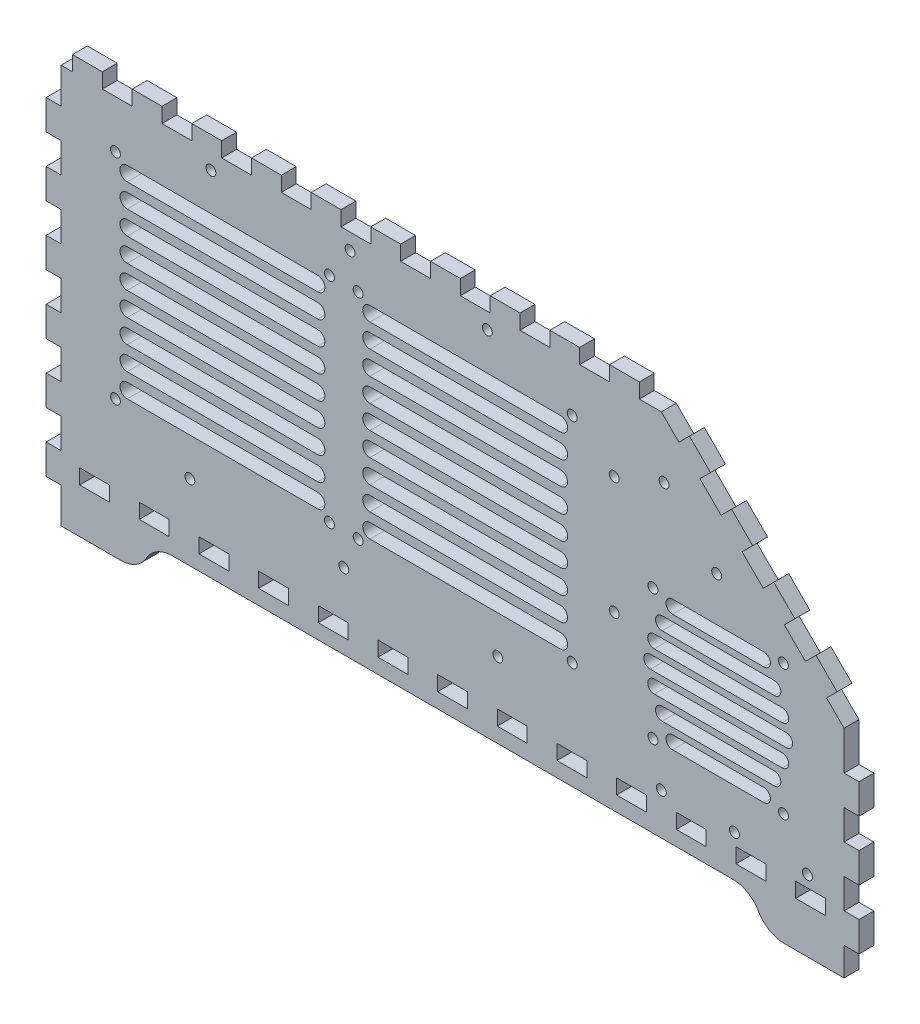
SolidWorks part; units mm, degrees
ref_plane "Front Plane" through (0, 0, 0) normal (0, 0, 1) x (1, 0, 0)
ref_plane "Top Plane" through (0, 0, 0) normal (0, 1, 0) x (1, 0, 0)
ref_plane "Right Plane" through (0, 0, 0) normal (1, 0, 0) x (0, 0, -1)
sketch "Model" plane through (0, 0, 0) normal (0, 0, 1) x (1, 0, 0)
  line L4 (28.9553, 40.0032) -> (23.2406, 40.0032)
  line L5 (23.2406, 40.0032) -> (23.2406, 45.7179)
  line L6 (23.2406, 45.7179) -> (34.67, 45.7179)
  line L7 (34.67, 45.7179) -> (34.67, 40.0032)
  line L8 (34.67, 40.0032) -> (28.9553, 40.0032)
  line L9 (51.8156, 40.0032) -> (46.0996, 40.0032)
  line L10 (46.0996, 40.0032) -> (46.0996, 45.7179)
  line L11 (46.0996, 45.7179) -> (57.5303, 45.7179)
  line L12 (57.5303, 45.7179) -> (57.5303, 40.0032)
  line L13 (57.5303, 40.0032) -> (51.8156, 40.0032)
  line L14 (74.6746, 40.0032) -> (68.9599, 40.0032)
  line L15 (68.9599, 40.0032) -> (68.9599, 45.7179)
  line L16 (68.9599, 45.7179) -> (80.3906, 45.7179)
  line L17 (80.3906, 45.7179) -> (80.3906, 40.0032)
  line L18 (80.3906, 40.0032) -> (74.6746, 40.0032)
  line L19 (97.5349, 40.0032) -> (91.8199, 40.0032)
  line L20 (91.8199, 40.0032) -> (91.8199, 45.7179)
  line L21 (91.8199, 45.7179) -> (103.25, 45.7179)
  line L22 (103.25, 45.7179) -> (103.25, 40.0032)
  line L23 (103.25, 40.0032) -> (97.5349, 40.0032)
  line L24 (120.395, 40.0032) -> (114.68, 40.0032)
  line L25 (114.68, 40.0032) -> (114.68, 45.7179)
  line L26 (114.68, 45.7179) -> (126.11, 45.7179)
  line L27 (126.11, 45.7179) -> (126.11, 40.0032)
  line L28 (126.11, 40.0032) -> (120.395, 40.0032)
  line L29 (143.255, 40.0032) -> (137.541, 40.0032)
  line L30 (137.541, 40.0032) -> (137.541, 45.7179)
  line L31 (137.541, 45.7179) -> (148.97, 45.7179)
  line L32 (148.97, 45.7179) -> (148.97, 40.0032)
  line L33 (148.97, 40.0032) -> (143.255, 40.0032)
  line L34 (166.116, 40.0032) -> (160.4, 40.0032)
  line L35 (160.4, 40.0032) -> (160.4, 45.7179)
  line L36 (160.4, 45.7179) -> (171.83, 45.7179)
  line L37 (171.83, 45.7179) -> (171.83, 40.0032)
  line L38 (171.83, 40.0032) -> (166.116, 40.0032)
  line L39 (188.975, 40.0032) -> (183.26, 40.0032)
  line L40 (183.26, 40.0032) -> (183.26, 45.7179)
  line L41 (183.26, 45.7179) -> (194.691, 45.7179)
  line L42 (194.691, 45.7179) -> (194.691, 40.0032)
  line L43 (194.691, 40.0032) -> (188.975, 40.0032)
  line L44 (211.835, 40.0032) -> (206.12, 40.0032)
  line L45 (206.12, 40.0032) -> (206.12, 45.7179)
  line L46 (206.12, 45.7179) -> (217.55, 45.7179)
  line L47 (217.55, 45.7179) -> (217.55, 40.0032)
  line L48 (217.55, 40.0032) -> (211.835, 40.0032)
  line L49 (234.695, 40.0032) -> (228.98, 40.0032)
  line L50 (228.98, 40.0032) -> (228.98, 45.7179)
  line L51 (228.98, 45.7179) -> (240.41, 45.7179)
  line L52 (240.41, 45.7179) -> (240.41, 40.0032)
  line L53 (240.41, 40.0032) -> (234.695, 40.0032)
  line L54 (257.555, 40.0032) -> (251.841, 40.0032)
  line L55 (251.841, 40.0032) -> (251.841, 45.7179)
  line L56 (251.841, 45.7179) -> (263.27, 45.7179)
  line L57 (263.27, 45.7179) -> (263.27, 40.0032)
  line L58 (263.27, 40.0032) -> (257.555, 40.0032)
  line L59 (280.416, 40.0032) -> (274.7, 40.0032)
  line L60 (274.7, 40.0032) -> (274.7, 45.7179)
  line L61 (274.7, 45.7179) -> (286.13, 45.7179)
  line L62 (286.13, 45.7179) -> (286.13, 40.0032)
  line L63 (286.13, 40.0032) -> (280.416, 40.0032)
  line L64 (303.275, 40.0032) -> (297.56, 40.0032)
  line L65 (297.56, 40.0032) -> (297.56, 45.7179)
  line L66 (297.56, 45.7179) -> (308.991, 45.7179)
  line L67 (308.991, 45.7179) -> (308.991, 40.0032)
  line L68 (308.991, 40.0032) -> (303.275, 40.0032)
  line L69 (16.1148, 22.8575) -> (38.9749, 22.8575)
  line L70 (38.9749, 22.8575) -> (39.3485, 22.8575)
  line L71 (39.3485, 22.8575) -> (40.4689, 22.9567)
  line L72 (40.4689, 22.9567) -> (41.9322, 23.2475)
  line L73 (41.9322, 23.2475) -> (43.3447, 23.7271)
  line L74 (43.3447, 23.7271) -> (44.366, 24.2025)
  line L75 (44.366, 24.2025) -> (44.6899, 24.3885)
  line L76 (44.6899, 24.3885) -> (44.8511, 24.4822)
  line L77 (44.8511, 24.4822) -> (45.3263, 24.7854)
  line L78 (45.3263, 24.7854) -> (45.9341, 25.2222)
  line L79 (45.9341, 25.2222) -> (46.5116, 25.6963)
  line L80 (46.5116, 25.6963) -> (47.056, 26.2062)
  line L81 (47.056, 26.2062) -> (47.5657, 26.7505)
  line L82 (47.5657, 26.7505) -> (48.0399, 27.3279)
  line L83 (48.0399, 27.3279) -> (48.4766, 27.9356)
  line L84 (48.4766, 27.9356) -> (48.7796, 28.411)
  line L85 (48.7796, 28.411) -> (48.8735, 28.5722)
  line L86 (48.8735, 28.5722) -> (48.9673, 28.7348)
  line L87 (48.9673, 28.7348) -> (49.2689, 29.2103)
  line L88 (49.2689, 29.2103) -> (49.7057, 29.818)
  line L89 (49.7057, 29.818) -> (50.1798, 30.3954)
  line L90 (50.1798, 30.3954) -> (50.6899, 30.9397)
  line L91 (50.6899, 30.9397) -> (51.2339, 31.4496)
  line L92 (51.2339, 31.4496) -> (51.8114, 31.9236)
  line L93 (51.8114, 31.9236) -> (52.4192, 32.3605)
  line L94 (52.4192, 32.3605) -> (52.8948, 32.6622)
  line L95 (52.8948, 32.6622) -> (53.0571, 32.756)
  line L96 (53.0571, 32.756) -> (53.3799, 32.9434)
  line L97 (53.3799, 32.9434) -> (54.4008, 33.4188)
  line L98 (54.4008, 33.4188) -> (55.8133, 33.8983)
  line L99 (55.8133, 33.8983) -> (57.2766, 34.1891)
  line L100 (57.2766, 34.1891) -> (58.3971, 34.287)
  line L101 (58.3971, 34.287) -> (58.7721, 34.287)
  line L102 (58.7721, 34.287) -> (273.458, 34.287)
  line L103 (273.458, 34.287) -> (273.831, 34.287)
  line L104 (273.831, 34.287) -> (274.952, 34.1891)
  line L105 (274.952, 34.1891) -> (276.415, 33.8983)
  line L106 (276.415, 33.8983) -> (277.828, 33.4188)
  line L107 (277.828, 33.4188) -> (278.849, 32.9434)
  line L108 (278.849, 32.9434) -> (279.172, 32.756)
  line L109 (279.172, 32.756) -> (279.334, 32.6636)
  line L110 (279.334, 32.6636) -> (279.809, 32.3605)
  line L111 (279.809, 32.3605) -> (280.417, 31.9236)
  line L112 (280.417, 31.9236) -> (280.995, 31.4496)
  line L113 (280.995, 31.4496) -> (281.539, 30.9397)
  line L114 (281.539, 30.9397) -> (282.049, 30.3954)
  line L115 (282.049, 30.3954) -> (282.523, 29.818)
  line L116 (282.523, 29.818) -> (282.96, 29.2103)
  line L117 (282.96, 29.2103) -> (283.263, 28.7348)
  line L118 (283.263, 28.7348) -> (283.356, 28.5722)
  line L119 (283.356, 28.5722) -> (283.449, 28.411)
  line L120 (283.449, 28.411) -> (283.752, 27.9356)
  line L121 (283.752, 27.9356) -> (284.189, 27.3279)
  line L122 (284.189, 27.3279) -> (284.663, 26.7505)
  line L123 (284.663, 26.7505) -> (285.172, 26.2062)
  line L124 (285.172, 26.2062) -> (285.717, 25.6963)
  line L125 (285.717, 25.6963) -> (286.294, 25.2222)
  line L126 (286.294, 25.2222) -> (286.902, 24.7854)
  line L127 (286.902, 24.7854) -> (287.377, 24.4822)
  line L128 (287.377, 24.4822) -> (287.54, 24.3885)
  line L129 (287.54, 24.3885) -> (287.862, 24.2025)
  line L130 (287.862, 24.2025) -> (288.884, 23.7271)
  line L131 (288.884, 23.7271) -> (290.296, 23.2475)
  line L132 (290.296, 23.2475) -> (291.76, 22.9567)
  line L133 (291.76, 22.9567) -> (292.88, 22.8575)
  line L134 (292.88, 22.8575) -> (293.255, 22.8575)
  line L135 (293.255, 22.8575) -> (316.115, 22.8575)
  line L136 (316.115, 22.8575) -> (316.115, 33.6917)
  line L137 (316.115, 33.6917) -> (321.83, 33.6917)
  line L138 (321.83, 33.6917) -> (321.83, 45.1224)
  line L139 (321.83, 45.1224) -> (316.115, 45.1224)
  line L140 (316.115, 45.1224) -> (316.115, 56.552)
  line L141 (316.115, 56.552) -> (321.83, 56.552)
  line L142 (321.83, 56.552) -> (321.83, 67.9813)
  line L143 (321.83, 67.9813) -> (316.115, 67.9813)
  line L144 (316.115, 67.9813) -> (316.115, 79.412)
  line L145 (316.115, 79.412) -> (321.83, 79.412)
  line L146 (321.83, 79.412) -> (321.83, 90.8417)
  line L147 (321.83, 90.8417) -> (316.115, 90.8417)
  line L148 (316.115, 90.8417) -> (316.115, 101.677)
  line L149 (316.115, 101.677) -> (316.115, 105.718)
  line L150 (316.115, 105.718) -> (309.403, 112.43)
  line L151 (309.403, 112.43) -> (313.444, 116.47)
  line L152 (313.444, 116.47) -> (305.362, 124.553)
  line L153 (305.362, 124.553) -> (301.321, 120.512)
  line L154 (301.321, 120.512) -> (293.238, 128.595)
  line L155 (293.238, 128.595) -> (297.28, 132.635)
  line L156 (297.28, 132.635) -> (289.198, 140.717)
  line L157 (289.198, 140.717) -> (285.156, 136.677)
  line L158 (285.156, 136.677) -> (277.074, 144.759)
  line L159 (277.074, 144.759) -> (281.114, 148.801)
  line L160 (281.114, 148.801) -> (273.032, 156.881)
  line L161 (273.032, 156.881) -> (268.992, 152.841)
  line L162 (268.992, 152.841) -> (260.91, 160.923)
  line L163 (260.91, 160.923) -> (264.951, 164.963)
  line L164 (264.951, 164.963) -> (256.869, 173.046)
  line L165 (256.869, 173.046) -> (252.827, 169.005)
  line L166 (252.827, 169.005) -> (246.115, 175.718)
  line L167 (246.115, 175.718) -> (242.074, 175.718)
  line L168 (242.074, 175.718) -> (237.68, 175.718)
  line L169 (237.68, 175.718) -> (237.68, 181.433)
  line L170 (237.68, 181.433) -> (226.249, 181.433)
  line L171 (226.249, 181.433) -> (226.249, 175.718)
  line L172 (226.249, 175.718) -> (214.82, 175.718)
  line L173 (214.82, 175.718) -> (214.82, 181.433)
  line L174 (214.82, 181.433) -> (203.389, 181.433)
  line L175 (203.389, 181.433) -> (203.389, 175.718)
  line L176 (203.389, 175.718) -> (191.959, 175.718)
  line L177 (191.959, 175.718) -> (191.959, 181.433)
  line L178 (191.959, 181.433) -> (180.53, 181.433)
  line L179 (180.53, 181.433) -> (180.53, 175.718)
  line L180 (180.53, 175.718) -> (169.099, 175.718)
  line L181 (169.099, 175.718) -> (169.099, 181.433)
  line L182 (169.099, 181.433) -> (157.67, 181.433)
  line L183 (157.67, 181.433) -> (157.67, 175.718)
  line L184 (157.67, 175.718) -> (146.239, 175.718)
  line L185 (146.239, 175.718) -> (146.239, 181.433)
  line L186 (146.239, 181.433) -> (134.809, 181.433)
  line L187 (134.809, 181.433) -> (134.809, 175.718)
  line L188 (134.809, 175.718) -> (123.38, 175.718)
  line L189 (123.38, 175.718) -> (123.38, 181.433)
  line L190 (123.38, 181.433) -> (111.949, 181.433)
  line L191 (111.949, 181.433) -> (111.949, 175.718)
  line L192 (111.949, 175.718) -> (100.52, 175.718)
  line L193 (100.52, 175.718) -> (100.52, 181.433)
  line L194 (100.52, 181.433) -> (89.0887, 181.433)
  line L195 (89.0887, 181.433) -> (89.0887, 175.718)
  line L196 (89.0887, 175.718) -> (77.6594, 175.718)
  line L197 (77.6594, 175.718) -> (77.6594, 181.433)
  line L198 (77.6594, 181.433) -> (66.2298, 181.433)
  line L199 (66.2298, 181.433) -> (66.2298, 175.718)
  line L200 (66.2298, 175.718) -> (54.7991, 175.718)
  line L201 (54.7991, 175.718) -> (54.7991, 181.433)
  line L202 (54.7991, 181.433) -> (43.3698, 181.433)
  line L203 (43.3698, 181.433) -> (43.3698, 175.718)
  line L204 (43.3698, 175.718) -> (31.9388, 175.718)
  line L205 (31.9388, 175.718) -> (31.9388, 181.433)
  line L206 (31.9388, 181.433) -> (20.5093, 181.433)
  line L207 (20.5093, 181.433) -> (20.5093, 175.718)
  line L208 (20.5093, 175.718) -> (16.1148, 175.718)
  line L209 (16.1148, 175.718) -> (16.1148, 162.153)
  line L210 (16.1148, 162.153) -> (10.4001, 162.153)
  line L211 (10.4001, 162.153) -> (10.4001, 150.723)
  line L212 (10.4001, 150.723) -> (16.1148, 150.723)
  line L213 (16.1148, 150.723) -> (16.1148, 139.292)
  line L214 (16.1148, 139.292) -> (10.4001, 139.292)
  line L215 (10.4001, 139.292) -> (10.4001, 127.863)
  line L216 (10.4001, 127.863) -> (16.1148, 127.863)
  line L217 (16.1148, 127.863) -> (16.1148, 116.433)
  line L218 (16.1148, 116.433) -> (10.4001, 116.433)
  line L219 (10.4001, 116.433) -> (10.4001, 105.003)
  line L220 (10.4001, 105.003) -> (16.1148, 105.003)
  line L221 (16.1148, 105.003) -> (16.1148, 93.5729)
  line L222 (16.1148, 93.5729) -> (10.4001, 93.5729)
  line L223 (10.4001, 93.5729) -> (10.4001, 82.1422)
  line L224 (10.4001, 82.1422) -> (16.1148, 82.1422)
  line L225 (16.1148, 82.1422) -> (16.1148, 70.7125)
  line L226 (16.1148, 70.7125) -> (10.4001, 70.7125)
  line L227 (10.4001, 70.7125) -> (10.4001, 59.2832)
  line L228 (10.4001, 59.2832) -> (16.1148, 59.2832)
  line L229 (16.1148, 59.2832) -> (16.1148, 47.8525)
  line L230 (16.1148, 47.8525) -> (10.4001, 47.8525)
  line L231 (10.4001, 47.8525) -> (10.4001, 36.4229)
  line L232 (10.4001, 36.4229) -> (16.1148, 36.4229)
  line L233 (16.1148, 36.4229) -> (16.1148, 22.8575)
extrude "Boss-Extrude1" add sketch "Model" along normal blind 5.715
sketch "Sketch1" plane through (0, 0, 0) normal (0, 0, -1) x (-1, 0, 0)
  line L0 (-267.8976, 115.7127) -> (-267.8976, 65.7127) construction
  line L1 (-292.8976, 115.7127) -> (-242.8976, 115.7127) construction
  line L2 (-292.8976, 115.7127) -> (-292.8976, 65.7127) construction
  line L3 (-292.8976, 65.7127) -> (-242.8976, 65.7127) construction
  line L4 (-242.8976, 115.7127) -> (-242.8976, 65.7127) construction
  line L5 (-285.3976, 113.2127) -> (-250.3976, 113.2127) construction
  line L6 (-285.3976, 115.7127) -> (-250.3976, 115.7127)
  line L7 (-285.3976, 110.7127) -> (-250.3976, 110.7127)
  line L8 (-289.3976, 103.2127) -> (-246.3976, 103.2127)
  line L9 (-289.3976, 108.2127) -> (-246.3976, 108.2127)
  line L10 (-289.3976, 105.7127) -> (-246.3976, 105.7127) construction
  line L11 (-292.3976, 95.7127) -> (-243.3976, 95.7127)
  line L12 (-292.3976, 100.7127) -> (-243.3976, 100.7127)
  line L13 (-292.3976, 98.2127) -> (-243.3976, 98.2127) construction
  line L14 (-293.8976, 88.2127) -> (-241.8976, 88.2127)
  line L15 (-293.8976, 93.2127) -> (-241.8976, 93.2127)
  line L16 (-293.8976, 90.7127) -> (-241.8976, 90.7127) construction
  line L17 (-292.3976, 80.7127) -> (-243.3976, 80.7127)
  line L18 (-292.3976, 85.7127) -> (-243.3976, 85.7127)
  line L19 (-292.3976, 83.2127) -> (-243.3976, 83.2127) construction
  line L20 (-289.3976, 73.2127) -> (-246.3976, 73.2127)
  line L21 (-289.3976, 78.2127) -> (-246.3976, 78.2127)
  line L22 (-289.3976, 75.7127) -> (-246.3976, 75.7127) construction
  line L23 (-285.3976, 65.7127) -> (-250.3976, 65.7127)
  line L24 (-285.3976, 70.7127) -> (-250.3976, 70.7127)
  line L25 (-285.3976, 68.2127) -> (-250.3976, 68.2127) construction
  line L26 (-279.0487, 113.2127) -> (-279.0487, 105.7127) construction
  line L27 (-279.0487, 105.7127) -> (-279.0487, 98.2127) construction
  line L28 (-279.0487, 98.2127) -> (-279.0487, 90.7127) construction
  line L29 (-279.0487, 90.7127) -> (-279.0487, 83.2127) construction
  line L30 (-279.0487, 83.2127) -> (-279.0487, 75.7127) construction
  arc A0 (-285.3976, 115.7127) -> (-285.3976, 110.7127) centre (-285.3976, 113.2127) ccw
  arc A1 (-250.3976, 110.7127) -> (-250.3976, 115.7127) centre (-250.3976, 113.2127) ccw
  arc A2 (-289.3976, 108.2127) -> (-289.3976, 103.2127) centre (-289.3976, 105.7127) ccw
  arc A3 (-246.3976, 103.2127) -> (-246.3976, 108.2127) centre (-246.3976, 105.7127) ccw
  arc A4 (-292.3976, 100.7127) -> (-292.3976, 95.7127) centre (-292.3976, 98.2127) ccw
  arc A5 (-243.3976, 95.7127) -> (-243.3976, 100.7127) centre (-243.3976, 98.2127) ccw
  arc A6 (-293.8976, 93.2127) -> (-293.8976, 88.2127) centre (-293.8976, 90.7127) ccw
  arc A7 (-241.8976, 88.2127) -> (-241.8976, 93.2127) centre (-241.8976, 90.7127) ccw
  arc A8 (-292.3976, 85.7127) -> (-292.3976, 80.7127) centre (-292.3976, 83.2127) ccw
  arc A9 (-243.3976, 80.7127) -> (-243.3976, 85.7127) centre (-243.3976, 83.2127) ccw
  arc A10 (-289.3976, 78.2127) -> (-289.3976, 73.2127) centre (-289.3976, 75.7127) ccw
  arc A11 (-246.3976, 73.2127) -> (-246.3976, 78.2127) centre (-246.3976, 75.7127) ccw
  arc A12 (-285.3976, 70.7127) -> (-285.3976, 65.7127) centre (-285.3976, 68.2127) ccw
  arc A13 (-250.3976, 65.7127) -> (-250.3976, 70.7127) centre (-250.3976, 68.2127) ccw
  point P10 (-267.8976, 113.2127)
  point P18 (-267.8976, 105.7127)
  point P25 (-267.8976, 98.2127)
  point P32 (-267.8976, 90.7127)
  point P39 (-267.8976, 83.2127)
  point P46 (-267.8976, 75.7127)
  point P53 (-267.8976, 68.2127)
  dimension "D3" = 2.5
  dimension "D1" = 35
  dimension "D2" = 2.5
  dimension "D4" = 2.5
  dimension "D7" = 43
  dimension "D9" = 49
  dimension "D13" = 52
extrude "Cut-Extrude1" cut sketch "Sketch1" against normal through all
hole_wizard "#6 Clearance Hole2" positions "Sketch2" profile "Sketch3" hole size "#6" standard "ANSI Inch" end condition through all
sketch "Sketch2" plane through (0, 0, 0) normal (0, 0, -1) x (-1, 0, 0)
  point P0 (-292.8976, 115.7127)
  point P3 (-242.8976, 115.7127)
  point P6 (-292.8976, 65.7127)
  point P9 (-242.8976, 65.7127)
sketch "Sketch3" plane through (292.8976, 115.7127, 0) normal (1, 0, 0) x (0, 1, 0)
  line L0 (0, 0) -> (0, 5.715)
  line L1 (0, 5.715) -> (1.8986, 5.715)
  line L2 (1.8986, 5.715) -> (1.8986, 0)
  line L5 (1.8986, 0) -> (0, 0)
  line L11 (0, -6.35) -> (0, 107.95) construction
  dimension "Thru Hole Dia." = 3.7973
  dimension "Thru Hole Depth" = 5.715
sketch "Sketch4" plane through (0, 0, 0) normal (0, 0, -1) x (-1, 0, 0)
  line L0 (-36.9564, 75.4325) -> (-211.9563, 75.4325) construction
  line L1 (-211.9563, 75.4325) -> (-211.9563, 157.4325) construction
  line L2 (-211.9563, 157.4325) -> (-129.9563, 157.4325) construction
  line L3 (-36.9564, 157.4325) -> (-36.9564, 75.4325) construction
  line L4 (-129.9563, 157.4325) -> (-129.9563, 75.4325) construction
  line L5 (-118.9564, 157.4325) -> (-118.9564, 75.4325) construction
  line L6 (-129.9563, 157.4325) -> (-118.9564, 157.4325) construction
  line L7 (-118.9564, 157.4325) -> (-36.9564, 157.4325) construction
  line L8 (-170.9563, 157.4325) -> (-170.9563, 75.4325) construction
  line L9 (-124.4563, 157.4325) -> (-124.4563, 75.4325) construction
  line L10 (-207.4563, 152.4325) -> (-134.4563, 152.4325) construction
  line L11 (-207.4563, 155.1825) -> (-134.4563, 155.1825)
  line L12 (-207.4563, 149.6825) -> (-134.4563, 149.6825)
  line L13 (-207.4563, 140.6825) -> (-134.4563, 140.6825)
  line L14 (-207.4563, 146.1825) -> (-134.4563, 146.1825)
  line L15 (-207.4563, 143.4325) -> (-134.4563, 143.4325) construction
  line L16 (-207.4563, 131.6825) -> (-134.4563, 131.6825)
  line L17 (-207.4563, 137.1825) -> (-134.4563, 137.1825)
  line L18 (-207.4563, 134.4325) -> (-134.4563, 134.4325) construction
  line L19 (-207.4563, 122.6825) -> (-134.4563, 122.6825)
  line L20 (-207.4563, 128.1825) -> (-134.4563, 128.1825)
  line L21 (-207.4563, 125.4325) -> (-134.4563, 125.4325) construction
  line L22 (-207.4563, 113.6825) -> (-134.4563, 113.6825)
  line L23 (-207.4563, 119.1825) -> (-134.4563, 119.1825)
  line L24 (-207.4563, 116.4325) -> (-134.4563, 116.4325) construction
  line L25 (-207.4563, 104.6825) -> (-134.4563, 104.6825)
  line L26 (-207.4563, 110.1825) -> (-134.4563, 110.1825)
  line L27 (-207.4563, 107.4325) -> (-134.4563, 107.4325) construction
  line L28 (-207.4563, 95.6825) -> (-134.4563, 95.6825)
  line L29 (-207.4563, 101.1825) -> (-134.4563, 101.1825)
  line L30 (-207.4563, 98.4325) -> (-134.4563, 98.4325) construction
  line L31 (-207.4563, 86.6825) -> (-134.4563, 86.6825)
  line L32 (-207.4563, 92.1825) -> (-134.4563, 92.1825)
  line L33 (-207.4563, 89.4325) -> (-134.4563, 89.4325) construction
  line L34 (-207.4563, 77.6825) -> (-134.4563, 77.6825)
  line L35 (-207.4563, 83.1825) -> (-134.4563, 83.1825)
  line L36 (-207.4563, 80.4325) -> (-134.4563, 80.4325) construction
  line L37 (-41.4564, 80.4325) -> (-114.4564, 80.4325) construction
  line L38 (-41.4564, 83.1825) -> (-114.4564, 83.1825)
  line L39 (-41.4564, 77.6825) -> (-114.4564, 77.6825)
  line L40 (-41.4564, 89.4325) -> (-114.4564, 89.4325) construction
  line L41 (-41.4564, 92.1825) -> (-114.4564, 92.1825)
  line L42 (-41.4564, 86.6825) -> (-114.4564, 86.6825)
  line L43 (-41.4564, 98.4325) -> (-114.4564, 98.4325) construction
  line L44 (-41.4564, 101.1825) -> (-114.4564, 101.1825)
  line L45 (-41.4564, 95.6825) -> (-114.4564, 95.6825)
  line L46 (-41.4564, 107.4325) -> (-114.4564, 107.4325) construction
  line L47 (-41.4564, 110.1825) -> (-114.4564, 110.1825)
  line L48 (-41.4564, 104.6825) -> (-114.4564, 104.6825)
  line L49 (-41.4564, 116.4325) -> (-114.4564, 116.4325) construction
  line L50 (-41.4564, 119.1825) -> (-114.4564, 119.1825)
  line L51 (-41.4564, 113.6825) -> (-114.4564, 113.6825)
  line L52 (-41.4564, 125.4325) -> (-114.4564, 125.4325) construction
  line L53 (-41.4564, 128.1825) -> (-114.4564, 128.1825)
  line L54 (-41.4564, 122.6825) -> (-114.4564, 122.6825)
  line L55 (-41.4564, 134.4325) -> (-114.4564, 134.4325) construction
  line L56 (-41.4564, 137.1825) -> (-114.4564, 137.1825)
  line L57 (-41.4564, 131.6825) -> (-114.4564, 131.6825)
  line L58 (-41.4564, 143.4325) -> (-114.4564, 143.4325) construction
  line L59 (-41.4564, 146.1825) -> (-114.4564, 146.1825)
  line L60 (-41.4564, 140.6825) -> (-114.4564, 140.6825)
  line L61 (-41.4564, 152.4325) -> (-114.4564, 152.4325) construction
  line L62 (-41.4564, 155.1825) -> (-114.4564, 155.1825)
  line L63 (-41.4564, 149.6825) -> (-114.4564, 149.6825)
  arc A0 (-207.4563, 155.1825) -> (-207.4563, 149.6825) centre (-207.4563, 152.4325) ccw
  arc A1 (-134.4563, 149.6825) -> (-134.4563, 155.1825) centre (-134.4563, 152.4325) ccw
  arc A2 (-207.4563, 146.1825) -> (-207.4563, 140.6825) centre (-207.4563, 143.4325) ccw
  arc A3 (-134.4563, 140.6825) -> (-134.4563, 146.1825) centre (-134.4563, 143.4325) ccw
  arc A4 (-207.4563, 137.1825) -> (-207.4563, 131.6825) centre (-207.4563, 134.4325) ccw
  arc A5 (-134.4563, 131.6825) -> (-134.4563, 137.1825) centre (-134.4563, 134.4325) ccw
  arc A6 (-207.4563, 128.1825) -> (-207.4563, 122.6825) centre (-207.4563, 125.4325) ccw
  arc A7 (-134.4563, 122.6825) -> (-134.4563, 128.1825) centre (-134.4563, 125.4325) ccw
  arc A8 (-207.4563, 119.1825) -> (-207.4563, 113.6825) centre (-207.4563, 116.4325) ccw
  arc A9 (-134.4563, 113.6825) -> (-134.4563, 119.1825) centre (-134.4563, 116.4325) ccw
  arc A10 (-207.4563, 110.1825) -> (-207.4563, 104.6825) centre (-207.4563, 107.4325) ccw
  arc A11 (-134.4563, 104.6825) -> (-134.4563, 110.1825) centre (-134.4563, 107.4325) ccw
  arc A12 (-207.4563, 101.1825) -> (-207.4563, 95.6825) centre (-207.4563, 98.4325) ccw
  arc A13 (-134.4563, 95.6825) -> (-134.4563, 101.1825) centre (-134.4563, 98.4325) ccw
  arc A14 (-207.4563, 92.1825) -> (-207.4563, 86.6825) centre (-207.4563, 89.4325) ccw
  arc A15 (-134.4563, 86.6825) -> (-134.4563, 92.1825) centre (-134.4563, 89.4325) ccw
  arc A16 (-207.4563, 83.1825) -> (-207.4563, 77.6825) centre (-207.4563, 80.4325) ccw
  arc A17 (-134.4563, 77.6825) -> (-134.4563, 83.1825) centre (-134.4563, 80.4325) ccw
  arc A18 (-41.4564, 83.1825) -> (-41.4564, 77.6825) centre (-41.4564, 80.4325) cw
  arc A19 (-114.4564, 77.6825) -> (-114.4564, 83.1825) centre (-114.4564, 80.4325) cw
  arc A20 (-41.4564, 92.1825) -> (-41.4564, 86.6825) centre (-41.4564, 89.4325) cw
  arc A21 (-114.4564, 86.6825) -> (-114.4564, 92.1825) centre (-114.4564, 89.4325) cw
  arc A22 (-41.4564, 101.1825) -> (-41.4564, 95.6825) centre (-41.4564, 98.4325) cw
  arc A23 (-114.4564, 95.6825) -> (-114.4564, 101.1825) centre (-114.4564, 98.4325) cw
  arc A24 (-41.4564, 110.1825) -> (-41.4564, 104.6825) centre (-41.4564, 107.4325) cw
  arc A25 (-114.4564, 104.6825) -> (-114.4564, 110.1825) centre (-114.4564, 107.4325) cw
  arc A26 (-41.4564, 119.1825) -> (-41.4564, 113.6825) centre (-41.4564, 116.4325) cw
  arc A27 (-114.4564, 113.6825) -> (-114.4564, 119.1825) centre (-114.4564, 116.4325) cw
  arc A28 (-41.4564, 128.1825) -> (-41.4564, 122.6825) centre (-41.4564, 125.4325) cw
  arc A29 (-114.4564, 122.6825) -> (-114.4564, 128.1825) centre (-114.4564, 125.4325) cw
  arc A30 (-41.4564, 137.1825) -> (-41.4564, 131.6825) centre (-41.4564, 134.4325) cw
  arc A31 (-114.4564, 131.6825) -> (-114.4564, 137.1825) centre (-114.4564, 134.4325) cw
  arc A32 (-41.4564, 146.1825) -> (-41.4564, 140.6825) centre (-41.4564, 143.4325) cw
  arc A33 (-114.4564, 140.6825) -> (-114.4564, 146.1825) centre (-114.4564, 143.4325) cw
  arc A34 (-41.4564, 155.1825) -> (-41.4564, 149.6825) centre (-41.4564, 152.4325) cw
  arc A35 (-114.4564, 149.6825) -> (-114.4564, 155.1825) centre (-114.4564, 152.4325) cw
  point P3 (-36.9564, 157.4325)
  point P4 (-129.9563, 157.4325)
  point P9 (-118.9564, 157.4325)
  point P11 (-129.9563, 75.4325)
  point P13 (-118.9564, 75.4325)
  point P26 (-170.9563, 152.4325)
  point P35 (-170.9563, 143.4325)
  point P42 (-170.9563, 134.4325)
  point P49 (-170.9563, 125.4325)
  point P56 (-170.9563, 116.4325)
  point P63 (-170.9563, 107.4325)
  point P70 (-170.9563, 98.4325)
  point P77 (-170.9563, 89.4325)
  point P84 (-170.9563, 80.4325)
  point P89 (-77.9564, 80.4325)
  point P96 (-77.9564, 89.4325)
  point P103 (-77.9564, 98.4325)
  point P110 (-77.9564, 107.4325)
  point P117 (-77.9564, 116.4325)
  point P124 (-77.9564, 125.4325)
  point P131 (-77.9564, 134.4325)
  point P138 (-77.9564, 143.4325)
  point P145 (-77.9564, 152.4325)
  dimension "D2" = 2.75
  dimension "D1" = 73
  dimension "D3" = 5
  dimension "D5" = 9
  dimension "D6" = 82
  dimension "D7" = 175
  dimension "D8" = 11
  dimension "D4" = 9
extrude "Cut-Extrude2" cut sketch "Sketch4" against normal blind 10
hole_wizard "#6 Clearance Hole1" positions "Sketch5" profile "Sketch6" hole size "#6" standard "ANSI Inch" end condition through all
sketch "Sketch5" plane through (0, 0, 0) normal (0, 0, -1) x (-1, 0, 0)
  point P0 (-211.9563, 157.4325)
  point P3 (-129.9563, 157.4325)
  point P6 (-118.9564, 157.4325)
  point P9 (-36.9564, 157.4325)
  point P12 (-36.9564, 75.4325)
  point P15 (-118.9564, 75.4325)
  point P18 (-129.9564, 75.4325)
  point P21 (-211.9563, 75.4325)
sketch "Sketch6" plane through (211.9563, 157.4325, 0) normal (1, 0, 0) x (0, 1, 0)
  line L0 (0, 0) -> (0, 5.715)
  line L1 (0, 5.715) -> (1.8986, 5.715)
  line L2 (1.8986, 5.715) -> (1.8986, 0)
  line L5 (1.8986, 0) -> (0, 0)
  line L11 (0, -6.35) -> (0, 107.95) construction
  dimension "Thru Hole Dia." = 3.7973
  dimension "Thru Hole Depth" = 5.715
sketch "Sketch7" plane through (0, 0, 0) normal (0, 0, -1) x (-1, 0, 0)
  point P0 (-179.4484, 169.575)
  point P1 (-126.8651, 169.575)
  point P3 (-73.5318, 169.575)
sketch "Sketch10" plane through (0, 0, 0) normal (0, 0, -1) x (-1, 0, 0)
  point P0 (-183.4563, 63.2127)
  point P1 (-124.4563, 63.2127)
  point P3 (-65.4563, 63.2127)
  point P5 (-228.0476, 145.2151)
  point P7 (-228.0476, 100.2151)
  point P9 (-247.1454, 152.7578)
  point P11 (-267.298, 132.6053)
  point P13 (-311.6141, 79.7127)
  point P15 (-274.1141, 50.2127)
  point P17 (-246.1141, 50.2127)
  point P19 (-302.1141, 50.2127)
hole_wizard "#6 Clearance Hole3" positions "Sketch8" profile "Sketch9" hole size "#6" standard "ANSI Inch" end condition through all
sketch "Sketch8" plane through (0, 0, 5.715) normal (0, 0, 1) x (1, 0, 0)
  point P0 (73.5318, 169.575)
  point P3 (126.8651, 169.575)
  point P6 (179.4484, 169.575)
  point P9 (65.4563, 63.2127)
  point P12 (183.4563, 63.2127)
  point P15 (124.4563, 63.2127)
  point P19 (228.0476, 145.2151)
  point P22 (228.0476, 100.2151)
  point P26 (246.1141, 50.2127)
  point P29 (274.1141, 50.2127)
  point P32 (302.1141, 50.2127)
  point P35 (267.298, 132.6053)
  point P38 (247.1454, 152.7578)
sketch "Sketch9" plane through (73.5318, 169.575, 5.715) normal (1, 0, 0) x (0, -1, 0)
  line L0 (0, 0) -> (0, 5.715)
  line L1 (0, 5.715) -> (1.8986, 5.715)
  line L2 (1.8986, 5.715) -> (1.8986, 0)
  line L5 (1.8986, 0) -> (0, 0)
  line L11 (0, -6.35) -> (0, 107.95) construction
  dimension "Thru Hole Dia." = 3.7973
  dimension "Thru Hole Depth" = 5.715
